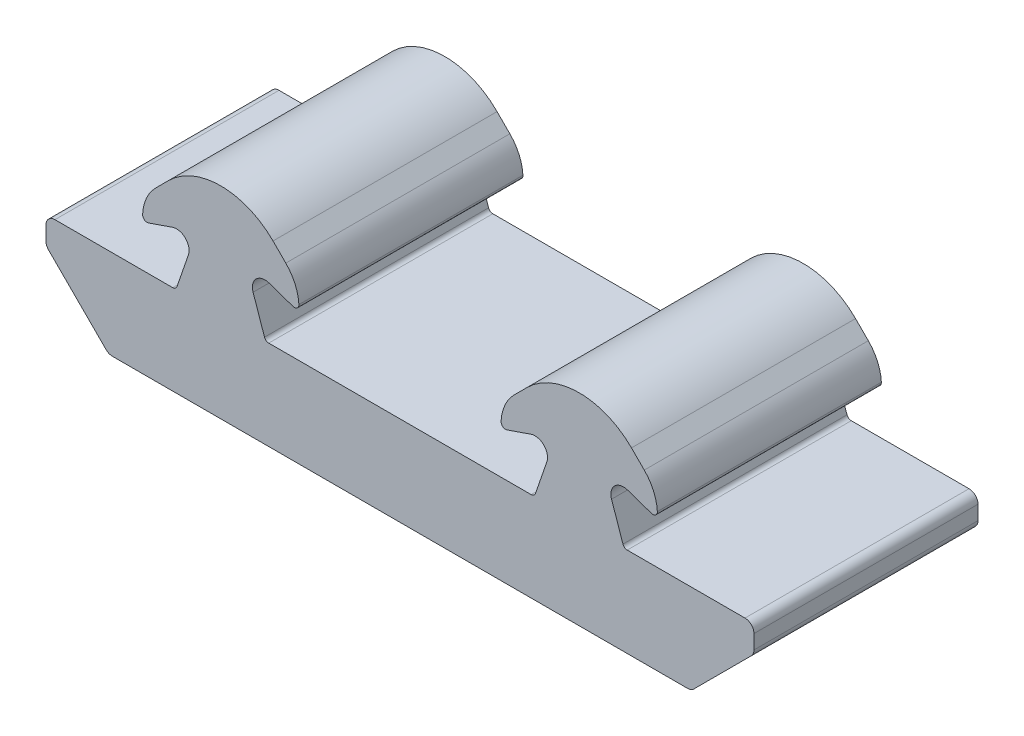
SolidWorks part; units mm, degrees
material "6005-T5"
ref_plane "Front" through (0, 0, 0) normal (0, 0, 1) x (1, 0, 0)
ref_plane "Top" through (0, 0, 0) normal (0, 1, 0) x (1, 0, 0)
ref_plane "Right" through (0, 0, 0) normal (1, 0, 0) x (0, 0, -1)
sketch "Sk Main Extrusion" plane through (0, 0, 0) normal (0, 0, 1) x (1, 0, 0)
  line L0 (-38.5, 4.8638) -> (-25.3566, 4.8638)
  line L5 (-39.5, 3.8638) -> (-39.5, 2.278)
  line L6 (39.5, 2.278) -> (39.5, 3.8638)
  line L7 (-23.6084, 8.9053) -> (-24.8839, 5.201)
  line L8 (-32.0858, -5.1362) -> (32.0858, -5.1362)
  line L9 (-28.0564, 9.766) -> (-25.3879, 10.6849)
  line L10 (0, -5.1362) -> (0, 0) construction
  line L11 (12.7395, 13.5455) -> (14.1664, 14.9724)
  line L12 (11.9436, 9.766) -> (14.6121, 10.6849)
  line L13 (16.3916, 8.9053) -> (15.1161, 5.201)
  line L14 (23.6084, 8.9053) -> (24.8839, 5.201)
  line L15 (28.0564, 9.766) -> (25.3879, 10.6849)
  line L16 (25.8336, 14.9724) -> (27.2605, 13.5455)
  line L17 (25.3566, 4.8638) -> (38.5, 4.8638)
  line L18 (-14.6434, 4.8638) -> (14.6434, 4.8638)
  line L19 (32.7929, -4.8433) -> (39.2071, 1.5709)
  line L20 (-32.7929, -4.8433) -> (-39.2071, 1.5709)
  line L21 (-20, 4.8638) -> (-20, 13.672) construction
  line L22 (-11.9436, 9.766) -> (-14.6121, 10.6849)
  line L23 (-16.3916, 8.9053) -> (-15.1161, 5.201)
  line L24 (-25.8336, 14.9724) -> (-27.2605, 13.5455)
  line L25 (-12.7395, 13.5455) -> (-14.1664, 14.9724)
  arc A0 (-15.1161, 5.201) -> (-14.6434, 4.8638) centre (-14.6434, 5.3638) ccw
  arc A1 (-11.9436, 9.766) -> (-11.2815, 10.2642) centre (-11.7808, 10.2388) ccw
  arc A2 (-24.8839, 5.201) -> (-25.3566, 4.8638) centre (-25.3566, 5.3638) cw
  arc A3 (-14.6121, 10.6849) -> (-16.3916, 8.9053) centre (-15.0679, 9.3611) ccw
  arc A4 (-28.0564, 9.766) -> (-28.7185, 10.2642) centre (-28.2192, 10.2388) cw
  arc A5 (-25.3879, 10.6849) -> (-23.6084, 8.9053) centre (-24.9321, 9.3611) cw
  arc A6 (-39.2071, 1.5709) -> (-39.5, 2.278) centre (-38.5, 2.278) cw
  arc A7 (-32.7929, -4.8433) -> (-32.0858, -5.1362) centre (-32.0858, -4.1362) ccw
  arc A8 (11.2815, 10.2642) -> (12.7395, 13.5455) centre (16.275, 10.01) cw
  arc A9 (39.5, 3.8638) -> (38.5, 4.8638) centre (38.5, 3.8638) ccw
  arc A10 (11.9436, 9.766) -> (11.2815, 10.2642) centre (11.7808, 10.2388) cw
  arc A11 (-39.5, 3.8638) -> (-38.5, 4.8638) centre (-38.5, 3.8638) cw
  arc A12 (14.6121, 10.6849) -> (16.3916, 8.9053) centre (15.0679, 9.3611) cw
  arc A13 (15.1161, 5.201) -> (14.6434, 4.8638) centre (14.6434, 5.3638) cw
  arc A14 (24.8839, 5.201) -> (25.3566, 4.8638) centre (25.3566, 5.3638) ccw
  arc A15 (25.3879, 10.6849) -> (23.6084, 8.9053) centre (24.9321, 9.3611) ccw
  arc A16 (28.0564, 9.766) -> (28.7185, 10.2642) centre (28.2192, 10.2388) ccw
  arc A17 (27.2605, 13.5455) -> (28.7185, 10.2642) centre (23.725, 10.01) cw
  arc A18 (14.1664, 14.9724) -> (25.8336, 14.9724) centre (20, 9.1388) cw
  arc A19 (39.2071, 1.5709) -> (39.5, 2.278) centre (38.5, 2.278) ccw
  arc A20 (32.0858, -5.1362) -> (32.7929, -4.8433) centre (32.0858, -4.1362) ccw
  arc A21 (-27.2605, 13.5455) -> (-28.7185, 10.2642) centre (-23.725, 10.01) ccw
  arc A22 (-14.1664, 14.9724) -> (-25.8336, 14.9724) centre (-20, 9.1388) ccw
  arc A23 (-11.2815, 10.2642) -> (-12.7395, 13.5455) centre (-16.275, 10.01) ccw
  point P38 (-11.7808, 9.7388)
extrude "Main Extrusion" add sketch "Sk Main Extrusion" against normal blind 25
equation "\"Weight kg\"= round ( \"SW-Mass\" , 2 )"
equation "\"Weight lbs\"= round ( \"SW-Mass\" * 2.2046 , 2 )"
equation "\"Length mm\"= round ( \"Length@Main Extrusion\" , 2 )"
equation "\"Length in\"= round ( \"Length@Main Extrusion\" / 25.4 , 3 )"
